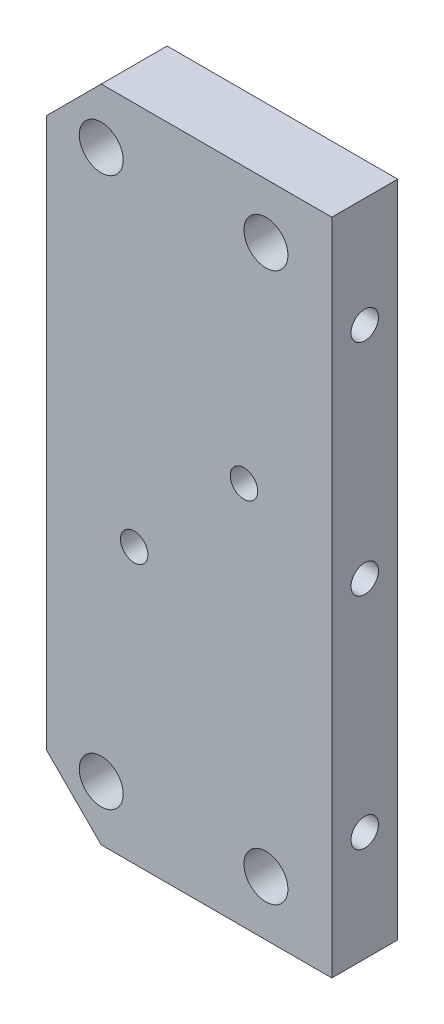
SolidWorks part; units mm, degrees
ref_plane "前视基准面" through (0, 0, 0) normal (0, 0, 1) x (1, 0, 0)
ref_plane "上视基准面" through (0, 0, 0) normal (0, 1, 0) x (1, 0, 0)
ref_plane "右视基准面" through (0, 0, 0) normal (1, 0, 0) x (0, 0, -1)
sketch "草图1" plane through (0, 0, 0) normal (0, 0, 1) x (1, 0, 0)
  line L1 (13, -30) -> (-13, -30)
  line L2 (13, -30) -> (13, 30)
  line L3 (13, 30) -> (-13, 30)
  line L4 (-13, -30) -> (-13, 30)
  line L5 (13, -30) -> (-13, 30) construction
  line L6 (13, 30) -> (-13, -30) construction
  point P0 (0, 0)
  dimension "D1" = 26
  dimension "D2" = 60
extrude "凸台-拉伸1" add sketch "草图1" along normal blind 6
sketch "草图2" plane through (0, 0, 0) normal (0, 0, -1) x (-1, 0, 0)
  circle A0 centre (8, -25) radius 2
  circle A1 centre (-7, -25) radius 2
  circle A2 centre (8, 25) radius 2
  circle A3 centre (-7, 25) radius 2
  dimension "D1" = 4
extrude "切除-拉伸1" cut sketch "草图2" against normal up to surface (6 mm away) up to face at (0, 0, 6)
hole_wizard "M3 螺纹孔1" positions "草图5" profile "草图6" tap size "M3" standard "GB"
sketch "草图5" plane through (13, 0, 0) normal (1, 0, 0) x (0, 0, -1)
  point P0 (-3, 20)
  point P5 (-3, 0)
  point P7 (-3, -20)
sketch "草图6" plane through (13, 20, 3) normal (0, 1, 0) x (0, 0, -1)
  line L0 (0, 0) -> (0, 8.2511)
  line L1 (0, 8.2511) -> (1.25, 7.5)
  line L2 (1.25, 7.5) -> (1.25, 0)
  line L5 (1.25, 0) -> (0, 0)
  line L10 (0, 8.2511) -> (-1.25, 7.5) construction
  line L11 (0, -6.35) -> (0, 107.95) construction
  dimension "螺纹孔钻头直径" = 2.5
  dimension "螺纹孔钻头深度" = 7.5
  dimension "导头角度" = 118
cosmetic thread "孔螺蚊线1" parameters "D1"=6, "D2"=3
cosmetic thread "孔螺蚊线2" parameters "D1"=6, "D2"=3
cosmetic thread "孔螺蚊线3" parameters "D1"=6, "D2"=3
chamfer "倒角1" distance 5 angle 45 2 edges at (-13, 30, 3) (-13, -30, 3)
hole_wizard "M3 螺纹孔2" positions "草图8" profile "草图9" tap size "M3" standard "GB"
sketch "草图8" plane through (0, 0, 6) normal (0, 0, 1) x (1, 0, 0)
  point P0 (5, 5)
  point P2 (-5, -5)
sketch "草图9" plane through (5, 5, 6) normal (1, 0, 0) x (0, -1, 0)
  line L0 (0, 0) -> (0, 8.2511)
  line L1 (0, 8.2511) -> (1.25, 7.5)
  line L2 (1.25, 7.5) -> (1.25, 0)
  line L5 (1.25, 0) -> (0, 0)
  line L10 (0, 8.2511) -> (-1.25, 7.5) construction
  line L11 (0, -6.35) -> (0, 107.95) construction
  dimension "螺纹孔钻头直径" = 2.5
  dimension "螺纹孔钻头深度" = 7.5
  dimension "导头角度" = 118
cosmetic thread "孔螺蚊线4" parameters "D1"=6, "D2"=3
cosmetic thread "孔螺蚊线5" parameters "D1"=6, "D2"=3
